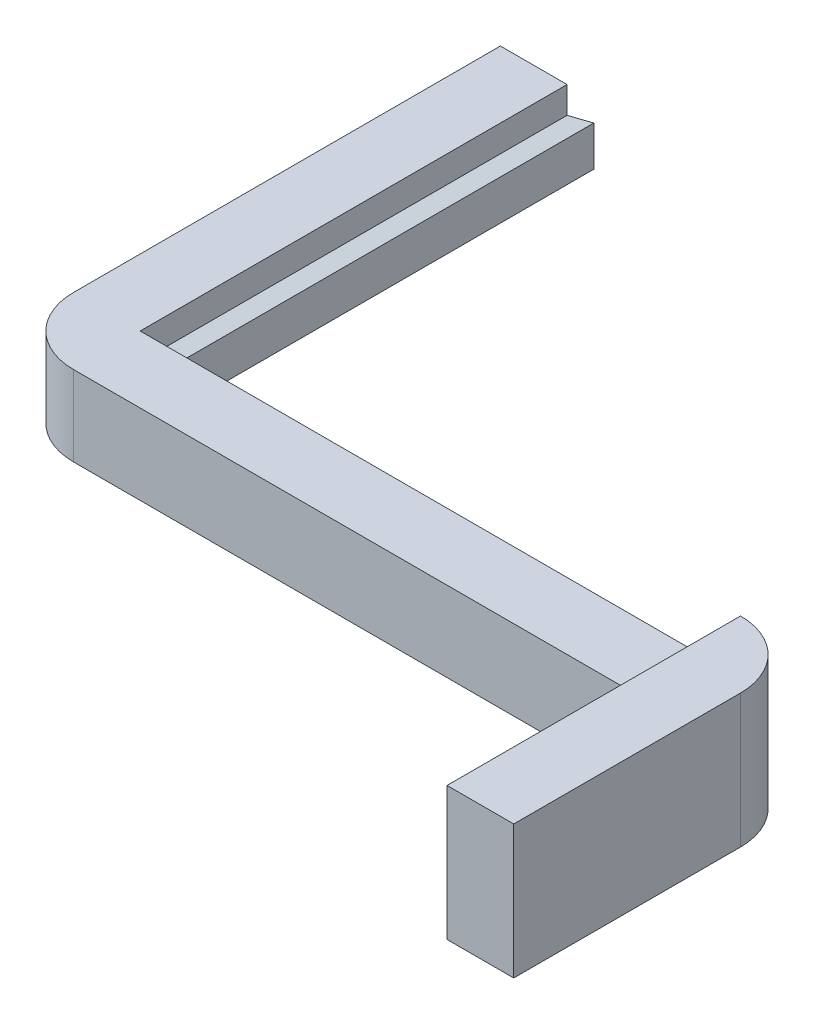
SolidWorks part; units mm, degrees
ref_plane "Front Plane" through (0, 0, 0) normal (0, 0, 1) x (1, 0, 0)
ref_plane "Top Plane" through (0, 0, 0) normal (0, 1, 0) x (1, 0, 0)
ref_plane "Right Plane" through (0, 0, 0) normal (1, 0, 0) x (0, 0, -1)
other "Configuration Table"
sketch "Sketch1" plane through (0, 0, 0) normal (0, 0, 1) x (1, 0, 0)
  line L1 (22.5, 3) -> (-22.5, 3)
  line L2 (22.5, 3) -> (22.5, -3)
  line L3 (22.5, -3) -> (-22.5, -3)
  line L4 (-22.5, 3) -> (-22.5, -3)
  line L5 (22.5, 3) -> (-22.5, -3) construction
  line L6 (22.5, -3) -> (-22.5, 3) construction
  point P0 (0, 0)
  dimension "D1" = 45
  dimension "D2" = 6
extrude "Boss-Extrude1" add sketch "Sketch1" along normal blind 5
sketch "Sketch2" plane through (-22.5, 0, 0) normal (-1, 0, 0) x (0, 0, 1)
  line L0 (5, -3) -> (0, -3) construction
  line L1 (5, 3) -> (-32, 3)
  line L2 (5, 3) -> (5, -3)
  line L3 (5, -3) -> (-32, -3)
  line L4 (-32, 3) -> (-32, -3)
  dimension "D1" = 37
extrude "Boss-Extrude2" add sketch "Sketch2" along normal blind 5
fillet "Fillet1" radius 5 1 edges at (-27.5, 0, 5)
sketch "Sketch3" plane through (22.5, 0, 0) normal (1, 0, 0) x (0, 0, -1)
  line L1 (0, 7) -> (-22, 7)
  line L2 (0, 7) -> (0, -3)
  line L3 (0, -3) -> (-22, -3)
  line L4 (-22, 7) -> (-22, -3)
  line L5 (-5, -3) -> (0, -3) construction
  line L6 (0, 13.6459) -> (0, -13.6459) construction
  dimension "D1" = 22
  dimension "D2" = 10
extrude "Boss-Extrude3" add sketch "Sketch3" along normal blind 5
fillet "Fillet2" radius 5 1 edges at (27.5, 2, 0)
sketch "Sketch4" plane through (-22.5, 0, 0) normal (1, 0, 0) x (0, 0, -1)
  line L1 (32, 3) -> (32, -3) construction
  line L3 (31, 2) -> (20, 2)
  line L4 (31, 2) -> (31, -2)
  line L5 (31, -2) -> (20, -2)
  line L6 (20, 2) -> (20, -2)
  line L7 (31, 2) -> (20, -2) construction
  line L8 (31, -2) -> (20, 2) construction
  line L9 (32, -3) -> (0, -3) construction
  point P0 (25.5, 0)
  dimension "D1" = 11
  dimension "D2" = 4
  dimension "D4" = 1
  dimension "D3" = 1
sketch "Sketch5" plane through (0, 0, 0) normal (0, 0, -1) x (-1, 0, 0)
  line L0 (22.5, 1) -> (20.5, 1.5)
  line L2 (20.5, 1.5) -> (20.5, -1.5)
  line L3 (20.5, -1.5) -> (22.5, -1)
  line L4 (22.5, 2) -> (22.5, -2) construction
  line L5 (22.5, 0) -> (12.4961, 0) construction
  line L6 (22.5, 3) -> (22.5, -3) construction
  line L7 (22.5, 1) -> (22.5, -1)
  dimension "D1" = 3
  dimension "D2" = 2
  dimension "D3" = 2
extrude "Boss-Extrude4" add sketch "Sketch5" along normal up to surface (32 mm away) contours L7 L3 L2 L0 up to face at (-25, 0, -32)
